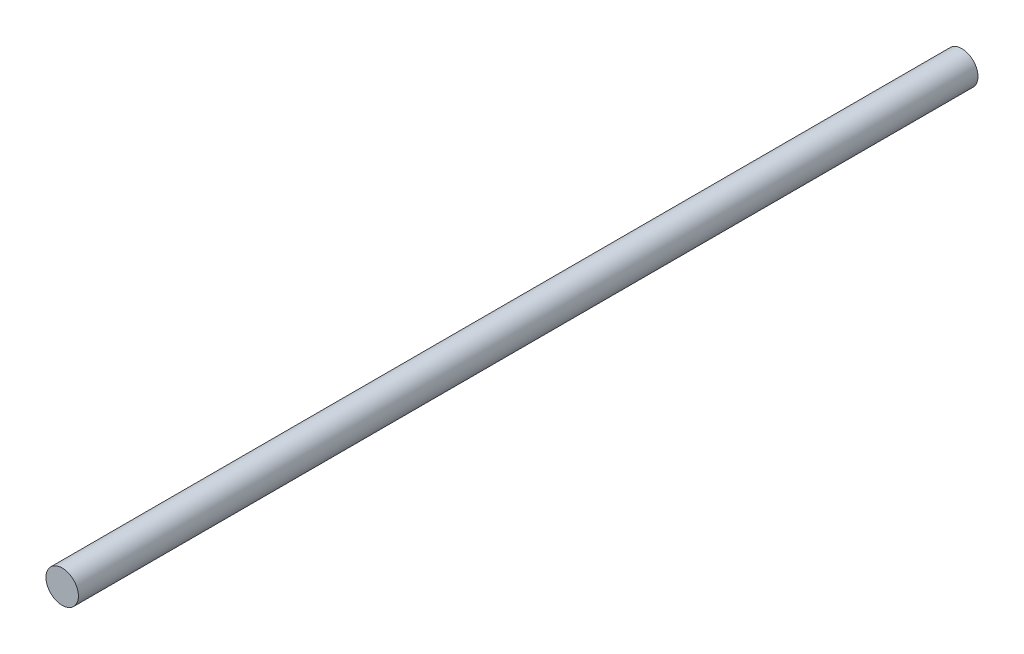
SolidWorks part; units mm, degrees
material "Plain Carbon Steel"
ref_plane "Front Plane" through (0, 0, 0) normal (0, 0, 1) x (1, 0, 0)
ref_plane "Top Plane" through (0, 0, 0) normal (0, 1, 0) x (1, 0, 0)
ref_plane "Right Plane" through (0, 0, 0) normal (1, 0, 0) x (0, 0, -1)
sketch "Sketch1" plane through (0, 0, 0) normal (0, 0, 1) x (1, 0, 0)
  circle A0 centre (0, 0) radius 5
  dimension "D1" = 10
extrude "Boss-Extrude1" add sketch "Sketch1" along normal blind 277.5
